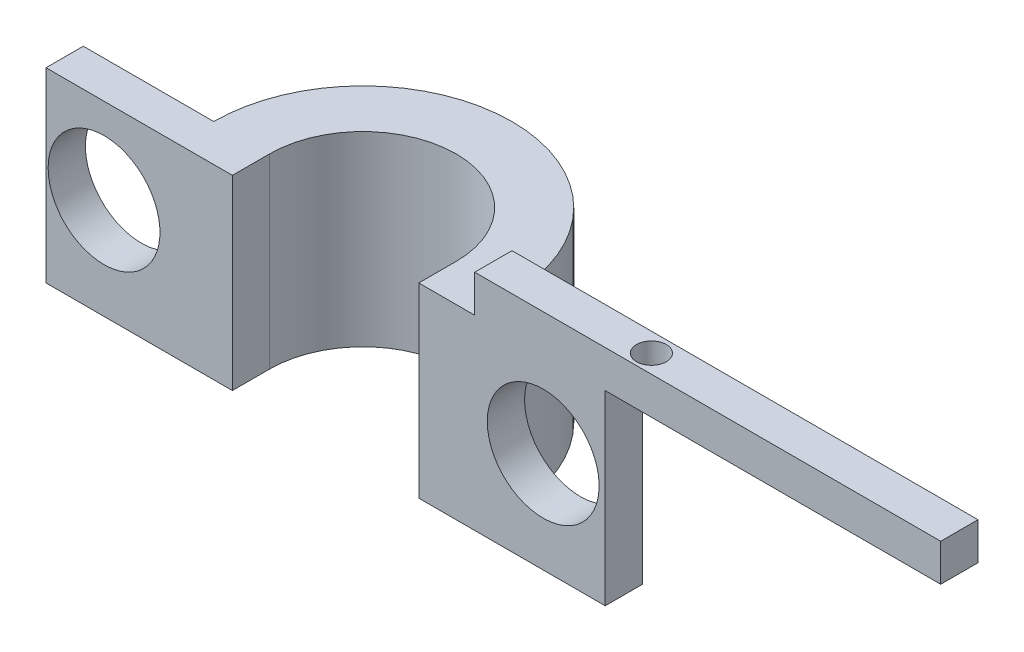
SolidWorks part; units mm, degrees
ref_plane "Front Plane" through (0, 0, 0) normal (0, 0, 1) x (1, 0, 0)
ref_plane "Top Plane" through (0, 0, 0) normal (0, 1, 0) x (1, 0, 0)
ref_plane "Right Plane" through (0, 0, 0) normal (1, 0, 0) x (0, 0, -1)
sketch "Sketch2" plane through (0, 0, 0) normal (0, 1, 0) x (1, 0, 0)
  circle A0 centre (0, 0) radius 5
extrude "Extrude-Thin1" add sketch "Sketch2" along normal blind 10 thin contours A0
sketch "Sketch3" plane through (0, 10, 0) normal (0, 1, 0) x (1, 0, 0)
  line L0 (-8, 0) -> (8, 0)
  circle A0 centre (0, 0) radius 8 construction
  arc A1 (-8, 0) -> (8, 0) centre (0, 0) ccw
extrude "Cut-Extrude1" cut sketch "Sketch3" against normal blind 10
sketch "Sketch4" plane through (0, 0, 0) normal (0, 0, 1) x (1, 0, 0)
  line L1 (5, 10) -> (15, 10)
  line L2 (5, 10) -> (5, 0)
  line L3 (5, 0) -> (15, 0)
  line L4 (15, 10) -> (15, 0)
  line L5 (-5, 10) -> (-15, 10)
  line L6 (-5, 10) -> (-5, 0)
  line L7 (-5, 0) -> (-15, 0)
  line L8 (-15, 10) -> (-15, 0)
  dimension "D1" = 10
  dimension "D2" = 10
extrude "Boss-Extrude1" add sketch "Sketch4" along normal blind 2
sketch "Sketch5" plane through (0, 0, 0) normal (0, 0, -1) x (-1, 0, 0)
  circle A0 centre (-11.6743, 5.4068) radius 3
  circle A1 centre (11.8859, 5.4068) radius 3
extrude "Cut-Extrude2" cut sketch "Sketch5" against normal blind 2
sketch "Sketch6" plane through (0, 10, 0) normal (0, 1, 0) x (1, 0, 0)
  line L1 (8, 0) -> (33, 0)
  line L2 (8, 0) -> (8, -2)
  line L3 (8, -2) -> (33, -2)
  line L4 (33, 0) -> (33, -2)
  dimension "D1" = 25
extrude "Boss-Extrude2" add sketch "Sketch6" along normal blind 2
sketch "Sketch7" plane through (0, 12, 0) normal (0, 1, 0) x (1, 0, 0)
  line L0 (33, -2) -> (33, 0) construction
  circle A0 centre (16.5, -1.0212) radius 0.8
  dimension "D1" = 16.5
extrude "Cut-Extrude3" cut sketch "Sketch7" against normal blind 2
